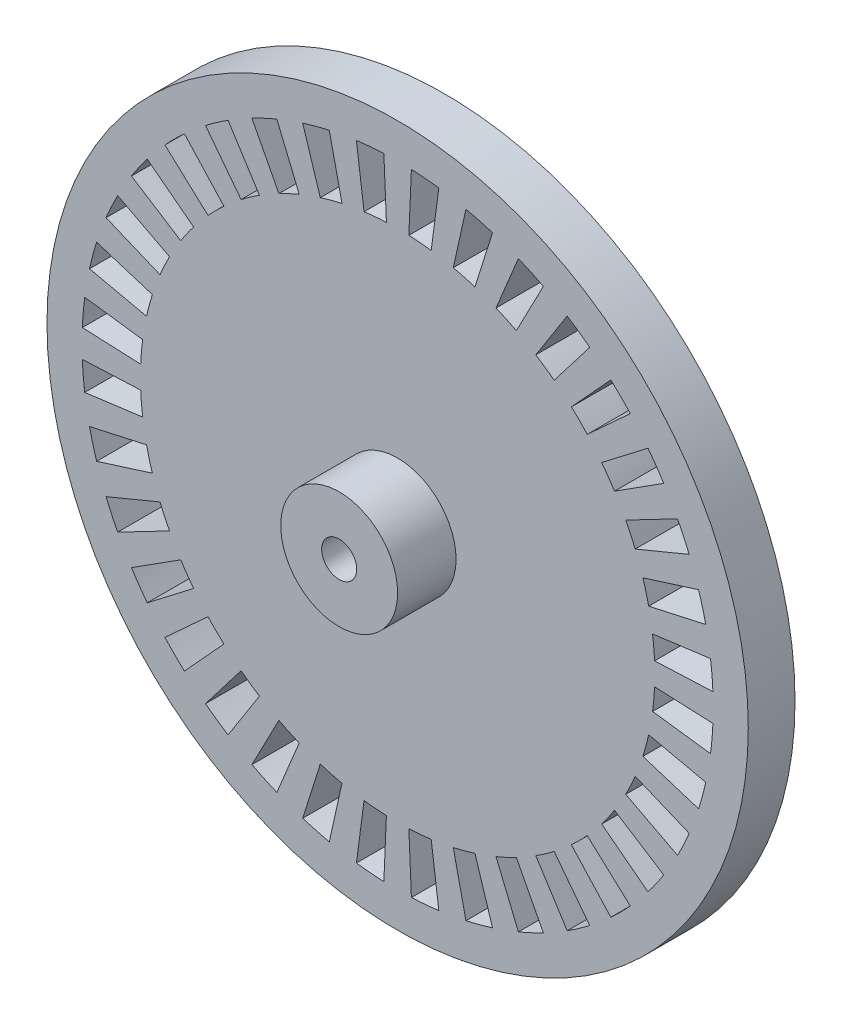
SolidWorks part; units mm, degrees
ref_plane "Plan de face" through (0, 0, 0) normal (0, 0, 1) x (1, 0, 0)
ref_plane "Plan de dessus" through (0, 0, 0) normal (0, 1, 0) x (1, 0, 0)
ref_plane "Plan de droite" through (0, 0, 0) normal (1, 0, 0) x (0, 0, -1)
sketch "Esquisse1" plane through (0, 0, 0) normal (0, 0, 1) x (1, 0, 0)
  line L0 (0, -30) -> (0, 30) construction
  line L1 (0, 0) -> (-26.9743, 1.1777) construction
  line L2 (30, 0) -> (-30, 0) construction
  line L3 (0, 0) -> (-26.9743, -1.1777) construction
  line L4 (0, 0) -> (-21.9791, 0.9596) construction
  line L5 (0, 0) -> (-21.9791, -0.9596) construction
  line L6 (-21.9791, 0.9596) -> (-26.9743, 1.1777)
  line L7 (-21.4785, 4.7617) -> (-26.36, 5.8439)
  line L8 (-21.9791, -0.9596) -> (-26.9743, -1.1777)
  line L9 (-21.8118, 2.8716) -> (-26.769, 3.5242)
  line L10 (-20.3253, 8.419) -> (-24.9447, 10.3325)
  line L11 (-20.9818, 6.6155) -> (-25.7504, 8.1191)
  line L12 (-18.5546, 11.8206) -> (-22.7716, 14.5071)
  line L13 (-19.5142, 10.1585) -> (-23.9493, 12.4672)
  line L14 (-16.2201, 14.863) -> (-19.9065, 18.2409)
  line L15 (-17.4538, 13.3928) -> (-21.4205, 16.4366)
  line L16 (-13.3928, 17.4538) -> (-16.4366, 21.4205)
  line L17 (-14.863, 16.2201) -> (-18.2409, 19.9065)
  line L18 (-10.1585, 19.5142) -> (-12.4672, 23.9493)
  line L19 (-11.8206, 18.5546) -> (-14.5071, 22.7716)
  line L20 (-6.6155, 20.9818) -> (-8.1191, 25.7504)
  line L21 (-8.419, 20.3253) -> (-10.3325, 24.9447)
  line L22 (-2.8716, 21.8118) -> (-3.5242, 26.769)
  line L23 (-4.7617, 21.4785) -> (-5.8439, 26.36)
  line L24 (0.9596, 21.9791) -> (1.1777, 26.9743)
  line L25 (-0.9596, 21.9791) -> (-1.1777, 26.9743)
  line L26 (4.7617, 21.4785) -> (5.8439, 26.36)
  line L27 (2.8716, 21.8118) -> (3.5242, 26.769)
  line L28 (8.419, 20.3253) -> (10.3325, 24.9447)
  line L29 (6.6155, 20.9818) -> (8.1191, 25.7504)
  line L30 (11.8206, 18.5546) -> (14.5071, 22.7716)
  line L31 (10.1585, 19.5142) -> (12.4672, 23.9493)
  line L32 (14.863, 16.2201) -> (18.2409, 19.9065)
  line L33 (13.3928, 17.4538) -> (16.4366, 21.4205)
  line L34 (17.4538, 13.3928) -> (21.4205, 16.4366)
  line L35 (16.2201, 14.863) -> (19.9065, 18.2409)
  line L36 (19.5142, 10.1585) -> (23.9493, 12.4672)
  line L37 (18.5546, 11.8206) -> (22.7716, 14.5071)
  line L38 (20.9818, 6.6155) -> (25.7504, 8.1191)
  line L39 (20.3253, 8.419) -> (24.9447, 10.3325)
  line L40 (21.8118, 2.8716) -> (26.769, 3.5242)
  line L41 (21.4785, 4.7617) -> (26.36, 5.8439)
  line L42 (21.9791, -0.9596) -> (26.9743, -1.1777)
  line L43 (21.9791, 0.9596) -> (26.9743, 1.1777)
  line L44 (21.4785, -4.7617) -> (26.36, -5.8439)
  line L45 (21.8118, -2.8716) -> (26.769, -3.5242)
  line L46 (20.3253, -8.419) -> (24.9447, -10.3325)
  line L47 (20.9818, -6.6155) -> (25.7504, -8.1191)
  line L48 (18.5546, -11.8206) -> (22.7716, -14.5071)
  line L49 (19.5142, -10.1585) -> (23.9493, -12.4672)
  line L50 (16.2201, -14.863) -> (19.9065, -18.2409)
  line L51 (17.4538, -13.3928) -> (21.4205, -16.4366)
  line L52 (13.3928, -17.4538) -> (16.4366, -21.4205)
  line L53 (14.863, -16.2201) -> (18.2409, -19.9065)
  line L54 (10.1585, -19.5142) -> (12.4672, -23.9493)
  line L55 (11.8206, -18.5546) -> (14.5071, -22.7716)
  line L56 (6.6155, -20.9818) -> (8.1191, -25.7504)
  line L57 (8.419, -20.3253) -> (10.3325, -24.9447)
  line L58 (2.8716, -21.8118) -> (3.5242, -26.769)
  line L59 (4.7617, -21.4785) -> (5.8439, -26.36)
  line L60 (-0.9596, -21.9791) -> (-1.1777, -26.9743)
  line L61 (0.9596, -21.9791) -> (1.1777, -26.9743)
  line L62 (-4.7617, -21.4785) -> (-5.8439, -26.36)
  line L63 (-2.8716, -21.8118) -> (-3.5242, -26.769)
  line L64 (-8.419, -20.3253) -> (-10.3325, -24.9447)
  line L65 (-6.6155, -20.9818) -> (-8.1191, -25.7504)
  line L66 (-11.8206, -18.5546) -> (-14.5071, -22.7716)
  line L67 (-10.1585, -19.5142) -> (-12.4672, -23.9493)
  line L68 (-14.863, -16.2201) -> (-18.2409, -19.9065)
  line L69 (-13.3928, -17.4538) -> (-16.4366, -21.4205)
  line L70 (-17.4538, -13.3928) -> (-21.4205, -16.4366)
  line L71 (-16.2201, -14.863) -> (-19.9065, -18.2409)
  line L72 (-19.5142, -10.1585) -> (-23.9493, -12.4672)
  line L73 (-18.5546, -11.8206) -> (-22.7716, -14.5071)
  line L74 (-20.9818, -6.6155) -> (-25.7504, -8.1191)
  line L75 (-20.3253, -8.419) -> (-24.9447, -10.3325)
  line L76 (-21.8118, -2.8716) -> (-26.769, -3.5242)
  line L77 (-21.4785, -4.7617) -> (-26.36, -5.8439)
  circle A0 centre (0, 0) radius 30
  circle A1 centre (0, 0) radius 27
  circle A2 centre (0, 0) radius 22
  circle A3 centre (0, 0) radius 1.5
  dimension "D1" = 60
  dimension "D2" = 3
  dimension "D3" = 5
  dimension "D6" = 3
  dimension "D4" = 2.5
  dimension "D5" = 36
extrude "Boss.-Extru.1" add sketch "Esquisse1" along normal blind 4 contours A2 | A0 A1 | A2 L6 A1 L8 | A2 L7 A1 L9 | A2 L10 A1 L11 | A2 L12 A1 L13 | A2 L14 A1 L15 | A2 L16 A1 L17 | A2 L18 A1 L19 | A2 L20 A1 L21 | A2 L22 A1 L23 | A2 L24 A1 L25 | A2 L26 A1 L27 | A2 L28 A1 L29 | A2 L30 A1 L31 | A2 L32 A1 L33 | A2 L34 A1 L35 | A2 L36 A1 L37 | A2 L38 A1 L39 | A2 L40 A1 L41 | A2 L42 A1 L43 | A2 L44 A1 L45 | A2 L46 A1 L47 | A2 L48 A1 L49 | A2 L50 A1 L51 | A2 L52 A1 L53 | A2 L54 A1 L55 | A2 L56 A1 L57 | A2 L58 A1 L59 | A2 L60 A1 L61 | A2 L62 A1 L63 | A2 L64 A1 L65 | A2 L66 A1 L67 | A2 L68 A1 L69 | A2 L70 A1 L71 | A2 L72 A1 L73 | A2 L74 A1 L75 | A2 L76 A1 L77
sketch "Esquisse2" plane through (0, 0, 4) normal (0, 0, 1) x (1, 0, 0)
  circle A0 centre (0, 0) radius 5
  circle A1 centre (0, 0) radius 1.5
  dimension "D1" = 10
  dimension "D2" = 3
extrude "Boss.-Extru.2" add sketch "Esquisse2" along normal blind 5
